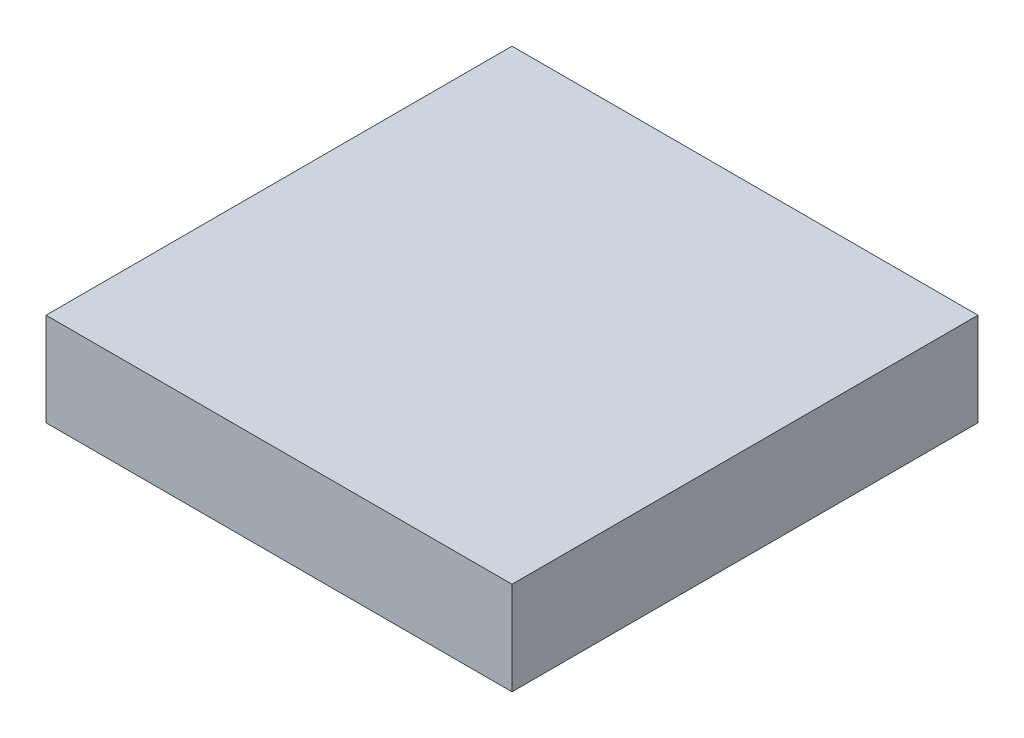
SolidWorks part; units mm, degrees
ref_plane "Front Plane" through (0, 0, 0) normal (0, 0, 1) x (1, 0, 0)
ref_plane "Top Plane" through (0, 0, 0) normal (0, 1, 0) x (1, 0, 0)
ref_plane "Right Plane" through (0, 0, 0) normal (1, 0, 0) x (0, 0, -1)
sketch "Sketch1" plane through (0, 0, 0) normal (0, 1, 0) x (1, 0, 0)
  line L1 (63.5, 63.5) -> (-63.5, 63.5)
  line L2 (63.5, 63.5) -> (63.5, -63.5)
  line L3 (63.5, -63.5) -> (-63.5, -63.5)
  line L4 (-63.5, 63.5) -> (-63.5, -63.5)
  line L5 (63.5, 63.5) -> (-63.5, -63.5) construction
  line L6 (63.5, -63.5) -> (-63.5, 63.5) construction
  point P0 (0, 0)
  dimension "D1" = 127
extrude "Boss-Extrude1" add sketch "Sketch1" along normal blind 25.4
